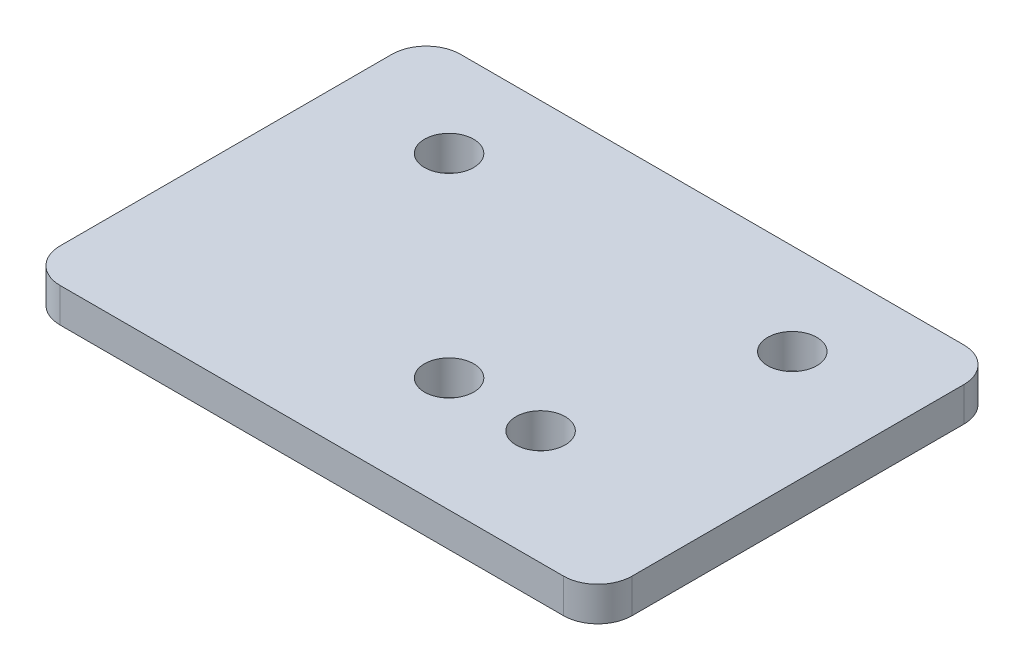
SolidWorks part; units mm, degrees
material "Thornel Mat VMA"
ref_plane "前视基准面" through (0, 0, 0) normal (0, 0, 1) x (1, 0, 0)
ref_plane "上视基准面" through (0, 0, 0) normal (0, 1, 0) x (1, 0, 0)
ref_plane "右视基准面" through (0, 0, 0) normal (1, 0, 0) x (0, 0, -1)
other "Configuration Table"
sketch "草图1" plane through (0, 0, 0) normal (0, 1, 0) x (1, 0, 0)
  line L1 (-25, -17.5) -> (25, -17.5)
  line L2 (-25, -17.5) -> (-25, 17.5)
  line L3 (-25, 17.5) -> (25, 17.5)
  line L4 (25, -17.5) -> (25, 17.5)
  line L5 (-25, -17.5) -> (25, 17.5) construction
  line L6 (-25, 17.5) -> (25, -17.5) construction
  point P0 (0, 0)
  dimension "D1" = 50
  dimension "D2" = 35
extrude "凸台-拉伸1" add sketch "草图1" along normal blind 3
sketch "草图2" plane through (0, 3, 0) normal (0, 1, 0) x (1, 0, 0)
  line L0 (0, 0) -> (0, 17.5) construction
  line L1 (25, 17.5) -> (-25, 17.5) construction
  circle A0 centre (-15, 9.5) radius 2.15
  circle A1 centre (15, 9.5) radius 2.15
  dimension "D1" = 4.3
  dimension "D2" = 8
  dimension "D3" = 30
extrude "切除-拉伸1" cut sketch "草图2" against normal blind 3
sketch "草图3" plane through (0, 3, 0) normal (0, 1, 0) x (1, 0, 0)
  line L0 (0, 0) -> (0, -17.5) construction
  line L1 (-25, -17.5) -> (25, -17.5) construction
  line L2 (25, -17.5) -> (25, 17.5) construction
  circle A0 centre (2, -7.5) radius 2.15
  circle A1 centre (10, -7.5) radius 2.15
  point P11 (0, 0)
  dimension "D1" = 4.3
  dimension "D2" = 8
  dimension "D3" = 10
  dimension "D4" = 15
extrude "切除-拉伸2" cut sketch "草图3" against normal blind 3
fillet "圆角1" radius 3 4 edges at (25, 1.5, 17.5) (-25, 1.5, -17.5) (25, 1.5, -17.5) (-25, 1.5, 17.5)
